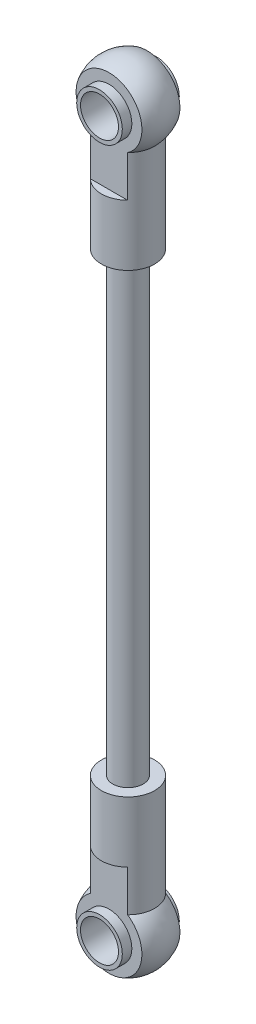
SolidWorks part; units mm, degrees
ref_plane "Front Plane" through (0, 0, 0) normal (0, 0, 1) x (1, 0, 0)
ref_plane "Top Plane" through (0, 0, 0) normal (0, 1, 0) x (1, 0, 0)
ref_plane "Right Plane" through (0, 0, 0) normal (1, 0, 0) x (0, 0, -1)
sketch "Sketch1" plane through (0, 0, 0) normal (0, 0, 1) x (1, 0, 0)
  line L0 (0, 0) -> (0, -7)
  line L1 (1.75, -17) -> (3.5, -17)
  line L2 (3.5, -17) -> (3.5, -3.5707)
  line L3 (0, 0) -> (0, 5)
  line L7 (0, -7) -> (1.75, -7)
  line L8 (1.75, -17) -> (1.75, -7)
  arc A0 (3.5, -3.5707) -> (0, 5) centre (0, 0) ccw
  dimension "D1" = 5
  dimension "D2" = 22
  dimension "D3" = 3.5
  dimension "D4" = 10
  dimension "D5" = 1.75
revolve "Revolve1" add sketch "Sketch1" angle 360 about L3
sketch "Sketch2" plane through (0, 0, 0) normal (0, 0, 1) x (1, 0, 0)
  circle A0 centre (0, 0) radius 2.5
  dimension "D1" = 5
extrude "Cut-Extrude1" cut sketch "Sketch2" against normal through all both and the other way through all
sketch "Sketch3" plane through (0, 0, 0) normal (0, 0, 1) x (1, 0, 0)
  circle A0 centre (0, 0) radius 2.5
ref_plane "Plane1" through (0, 0, 2.5) normal (0, 0, 1) x (1, 0, 0)
sketch "Sketch4" plane through (0, 0, 2.5) normal (0, 0, 1) x (1, 0, 0)
  line L1 (-6, -9) -> (6, -9)
  line L2 (-6, -9) -> (-6, 9)
  line L3 (-6, 9) -> (6, 9)
  line L4 (6, -9) -> (6, 9)
  line L5 (-6, -9) -> (6, 9) construction
  line L6 (-6, 9) -> (6, -9) construction
  point P0 (0, 0)
  dimension "D1" = 18
  dimension "D2" = 12
extrude "Cut-Extrude2" cut sketch "Sketch4" along normal up to next
mirror "Mirror1" about plane through (0, 0, 0) normal (0, 0, 1) of "Cut-Extrude2"
extrude "Extrude-Thin1" add sketch "Sketch3" along normal mid plane 7.5 thin
ref_plane "Plane2" through (0, -47, 0) normal (0, -1, 0) x (-1, 0, 0)
mirror "Mirror3" about plane through (0, -47, 0) normal (0, -1, 0) of bodies 105
sketch "Sketch5" plane through (0, -47, 0) normal (0, -1, 0) x (-1, 0, 0)
  circle A0 centre (0, 0) radius 2
  dimension "D1" = 4
extrude "Boss-Extrude1" add sketch "Sketch5" along normal mid plane 60
sketch "Sketch6" plane through (0, 0, -2.5) normal (0, 0, -1) x (-1, 0, 0)
  line L0 (0, -94) -> (0, 0)
  point P4 (0, 0)
